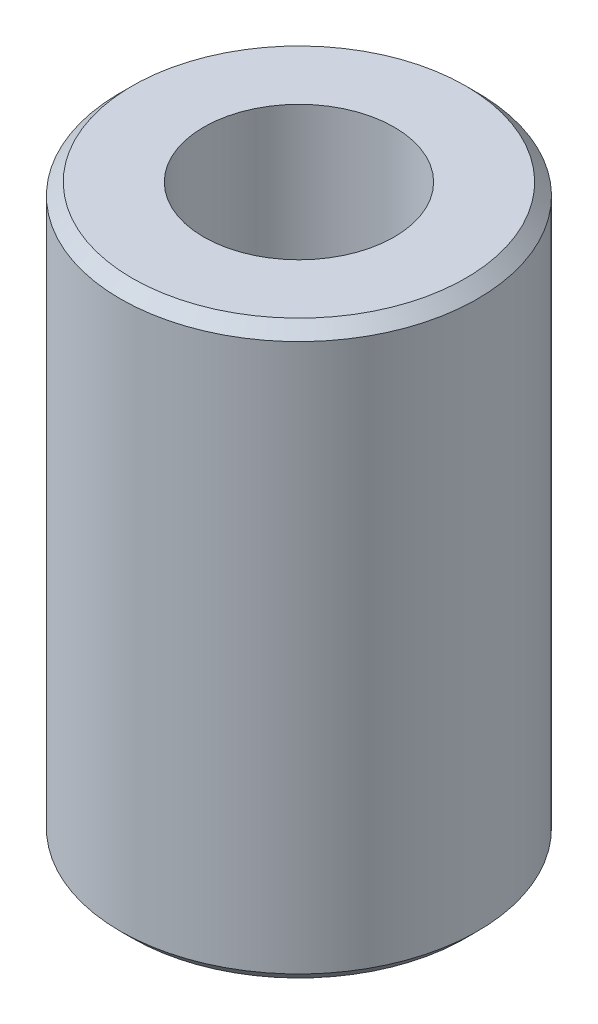
SolidWorks part; units mm, degrees
ref_plane "Front Plane" through (0, 0, 0) normal (0, 0, 1) x (1, 0, 0)
ref_plane "Top Plane" through (0, 0, 0) normal (0, 1, 0) x (1, 0, 0)
ref_plane "Right Plane" through (0, 0, 0) normal (1, 0, 0) x (0, 0, -1)
sketch "Sketch1" plane through (0, 0, 0) normal (0, 1, 0) x (1, 0, 0)
  circle A0 centre (0, 0) radius 7.5
  circle A1 centre (0, 0) radius 4
  dimension "D1" = 15
  dimension "D2" = 8
extrude "Boss-Extrude1" add sketch "Sketch1" along normal blind 24
chamfer "Chamfer1" distance 0.5 angle 45 2 edges at (0, 24, 7.5) (0, 0, 7.5)
